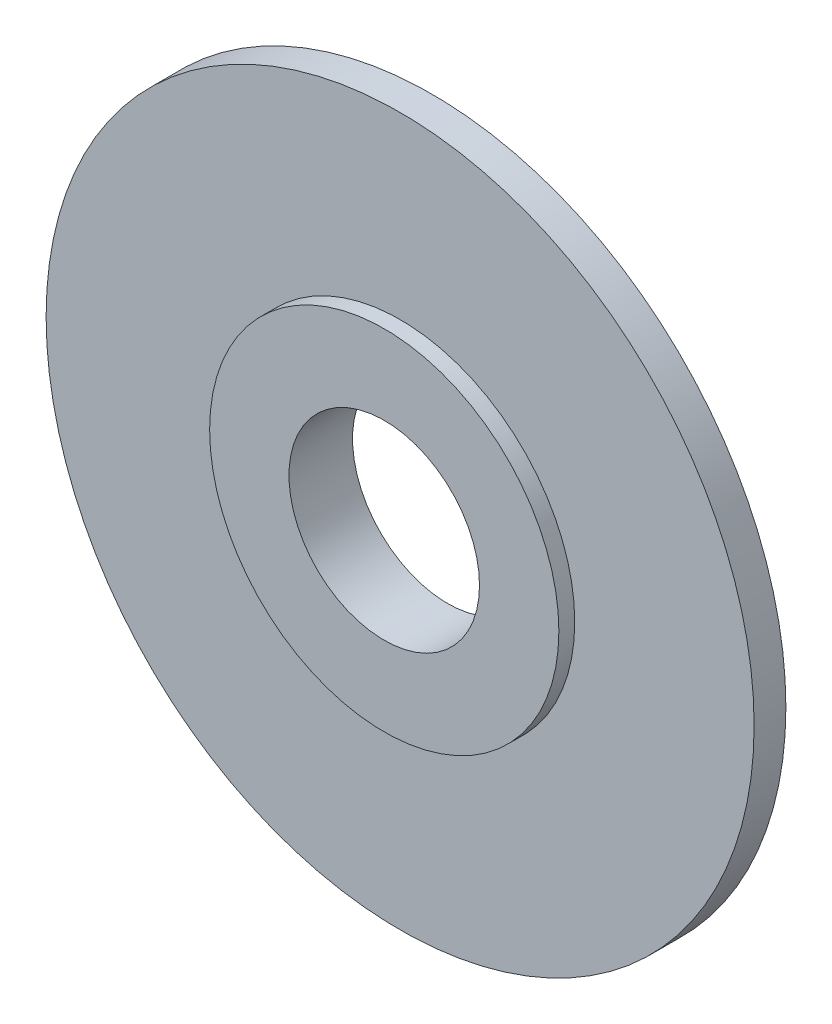
SolidWorks part; units mm, degrees
ref_plane "Front Plane" through (0, 0, 0) normal (0, 0, 1) x (1, 0, 0)
ref_plane "Top Plane" through (0, 0, 0) normal (0, 1, 0) x (1, 0, 0)
ref_plane "Right Plane" through (0, 0, 0) normal (1, 0, 0) x (0, 0, -1)
sketch "Sketch1" plane through (0, 0, 0) normal (0, 0, 1) x (1, 0, 0)
  line L0 (-49.9732, 0) -> (51.8439, 0) construction
  line L1 (0, 38.0812) -> (0, -46.6328) construction
  circle A0 centre (0, 0) radius 15
  circle A1 centre (0, 0) radius 27.5
  dimension "D1" = 55
  dimension "D2" = 30
extrude "Boss-Extrude1" add sketch "Sketch1" along normal blind 10
ref_plane "Plane1" through (0, 0, 5) normal (0, 0, 1) x (1, 0, 0)
sketch "Sketch2" plane through (0, 0, 5) normal (0, 0, 1) x (1, 0, 0)
  circle A0 centre (0, 0) radius 55.75
  circle A1 centre (0, 0) radius 27.5
extrude "Boss-Extrude2" add sketch "Sketch2" along normal blind 2.5 and the other way blind 2.5
